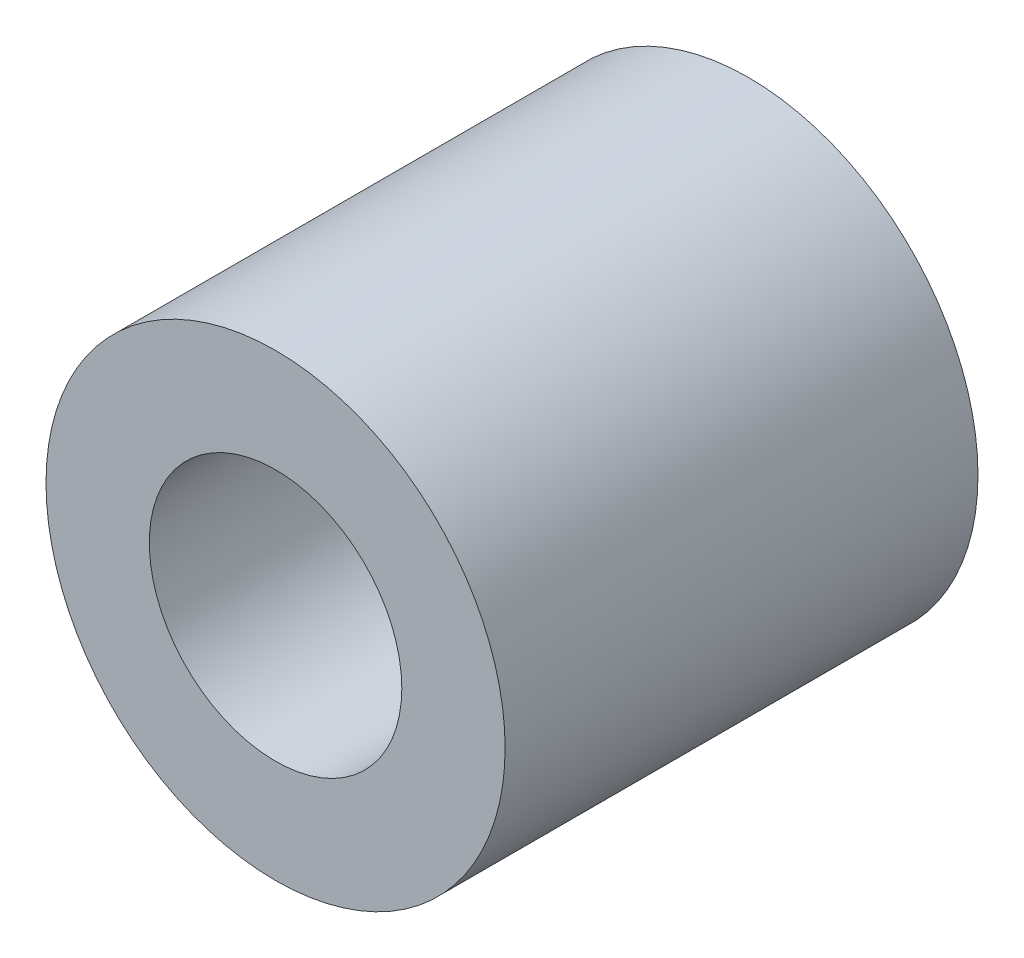
SolidWorks part; units mm, degrees
ref_plane "Front Plane" through (0, 0, 0) normal (0, 0, 1) x (1, 0, 0)
ref_plane "Top Plane" through (0, 0, 0) normal (0, 1, 0) x (1, 0, 0)
ref_plane "Right Plane" through (0, 0, 0) normal (1, 0, 0) x (0, 0, -1)
sketch "Sketch1" plane through (0, 0, 0) normal (0, 0, 1) x (1, 0, 0)
  circle A0 centre (0, 0) radius 1.1
  circle A1 centre (0, 0) radius 2
  dimension "D1" = 4
  dimension "D2" = 2.2
extrude "Boss-Extrude1" add sketch "Sketch1" along normal blind 4.12
